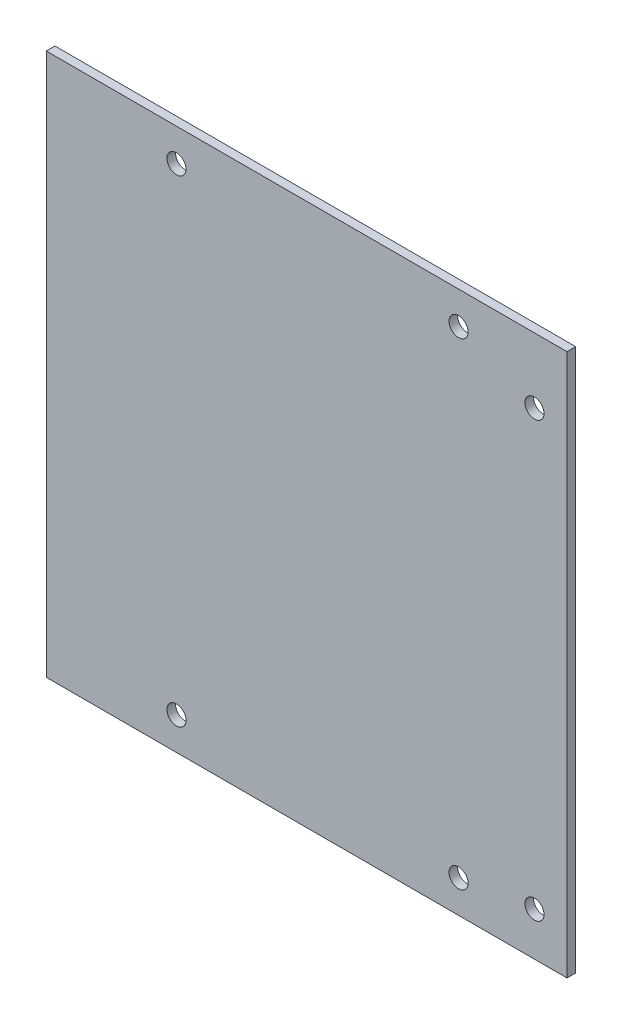
SolidWorks part; units mm, degrees
ref_plane "正面" through (0, 0, 0) normal (0, 0, 1) x (1, 0, 0)
ref_plane "平面" through (0, 0, 0) normal (0, 1, 0) x (1, 0, 0)
ref_plane "右側面" through (0, 0, 0) normal (1, 0, 0) x (0, 0, -1)
sketch "ｽｹｯﾁ1" plane through (0, 0, 0) normal (0, 0, 1) x (1, 0, 0)
  line L1 (-70, 62.5) -> (70, 62.5)
  line L2 (-70, 62.5) -> (-70, -62.5)
  line L3 (-70, -62.5) -> (70, -62.5)
  line L4 (70, 62.5) -> (70, -62.5)
  line L5 (-70, 62.5) -> (70, -62.5) construction
  line L6 (-70, -62.5) -> (70, 62.5) construction
  point P0 (0, 0)
  dimension "D1" = 125
  dimension "D2" = 140
extrude "ﾎﾞｽ - 押し出し1" add sketch "ｽｹｯﾁ1" along normal blind 2
sketch "ｽｹｯﾁ3" plane through (0, 0, 2) normal (0, 0, 1) x (1, 0, 0)
  line L0 (-70, 62.5) -> (-60, 62.5)
  line L1 (70, 62.5) -> (-70, 62.5) construction
  line L2 (-60, 62.5) -> (-60, 58.5)
  line L3 (-60, 58.5) -> (-60, -47.5)
  circle A0 centre (-60, 58.5) radius 2.2
  circle A1 centre (-60, -47.5) radius 2.2
  dimension "D4" = 4.4
  dimension "D5" = 4.4
  dimension "D1" = 10
  dimension "D2" = 4
  dimension "D3" = 106
extrude "ｶｯﾄ - 押し出し1" cut sketch "ｽｹｯﾁ3" against normal blind 2
sketch "ｽｹｯﾁ6" plane through (0, 0, 2) normal (0, 0, 1) x (1, 0, 0)
  line L0 (70, -62.5) -> (62.5, -62.5)
  line L1 (-70, -62.5) -> (70, -62.5) construction
  line L2 (62.5, -62.5) -> (62.5, -52.5)
  line L3 (62.5, -52.5) -> (62.5, 47.5)
  circle A0 centre (62.5, -52.5) radius 2.2
  circle A1 centre (62.5, 47.5) radius 2.2
  dimension "D3" = 4.4
  dimension "D5" = 4.4
  dimension "D1" = 7.5
  dimension "D2" = 10
  dimension "D4" = 100
extrude "ｶｯﾄ - 押し出し2" cut sketch "ｽｹｯﾁ6" against normal blind 2
sketch "ｽｹｯﾁ7" plane through (0, 0, 2) normal (0, 0, 1) x (1, 0, 0)
  line L0 (70, 62.5) -> (70, 55)
  line L1 (70, -62.5) -> (70, 62.5) construction
  line L2 (70, 55) -> (45, 55)
  line L3 (45, 55) -> (-20, 55)
  line L4 (70, -62.5) -> (70, -55)
  line L6 (70, -55) -> (45, -55)
  line L7 (45, -55) -> (-20, -55)
  circle A0 centre (45, 55) radius 2.2
  circle A1 centre (-20, 55) radius 2.2
  circle A2 centre (45, -55) radius 2.2
  circle A3 centre (-20, -55) radius 2.2
  dimension "D3" = 4.4
  dimension "D5" = 4.4
  dimension "D9" = 4.4
  dimension "D10" = 4.4
  dimension "D1" = 7.5
  dimension "D2" = 25
  dimension "D4" = 65
  dimension "D6" = 7.5
  dimension "D7" = 25
  dimension "D8" = 65
extrude "ｶｯﾄ - 押し出し3" cut sketch "ｽｹｯﾁ7" against normal blind 105 contours L2 A0 L3 | L3 A0 L2 | A1 | A2 | A3
sketch "ｽｹｯﾁ9" plane through (-70, 0, 0) normal (-1, 0, 0) x (0, 0, 1)
  line L1 (2, 62.5) -> (0, 62.5)
  line L2 (2, 62.5) -> (2, -62.5)
  line L3 (2, -62.5) -> (0, -62.5)
  line L4 (0, 62.5) -> (0, -62.5)
extrude "ｶｯﾄ - 押し出し5" cut sketch "ｽｹｯﾁ9" against normal blind 20
